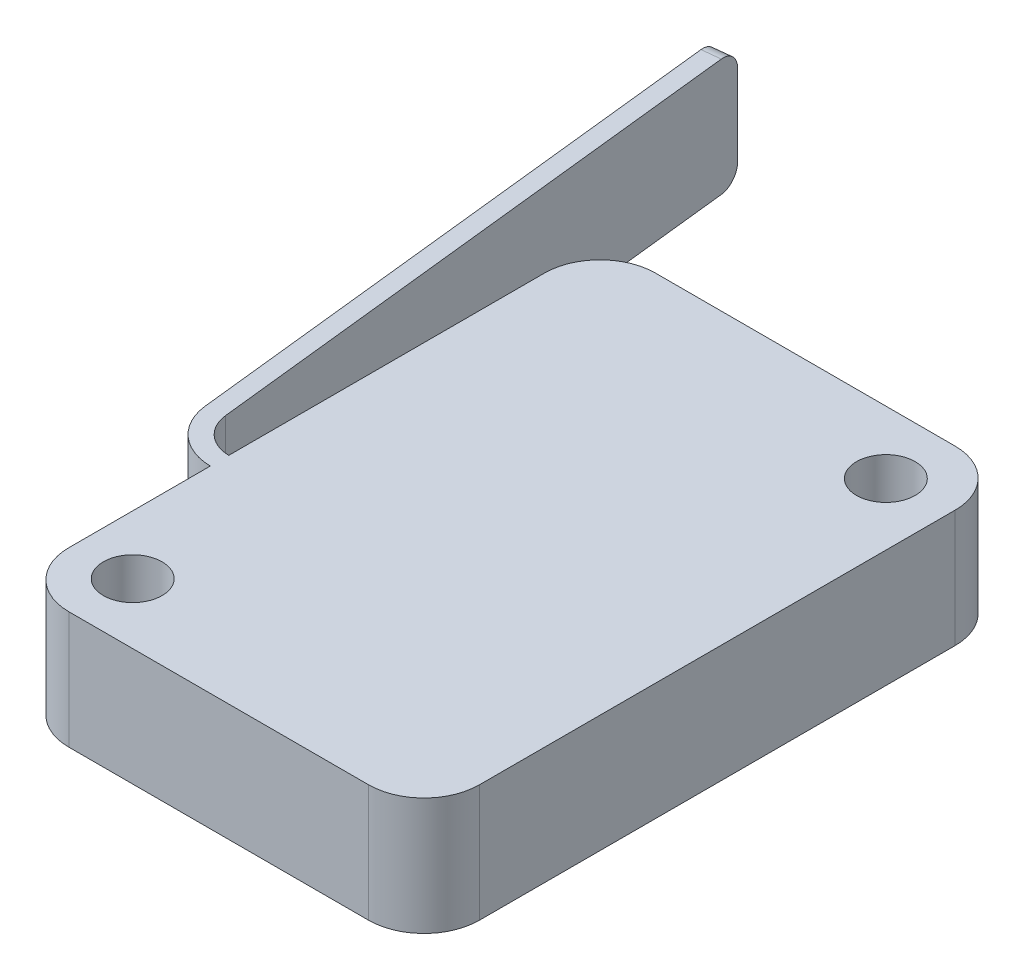
SolidWorks part; units mm, degrees
ref_plane "Front Plane" through (0, 0, 0) normal (0, 0, 1) x (1, 0, 0)
ref_plane "Top Plane" through (0, 0, 0) normal (0, 1, 0) x (1, 0, 0)
ref_plane "Right Plane" through (0, 0, 0) normal (1, 0, 0) x (0, 0, -1)
sketch "Sketch1" plane through (0, 0, 0) normal (0, 1, 0) x (1, 0, 0)
  line L1 (-11.1125, -15.875) -> (11.1125, -15.875)
  line L2 (-11.1125, -15.875) -> (-11.1125, 15.875)
  line L3 (-11.1125, 15.875) -> (11.1125, 15.875)
  line L4 (11.1125, -15.875) -> (11.1125, 15.875)
  line L5 (-11.1125, -15.875) -> (11.1125, 15.875) construction
  line L6 (-11.1125, 15.875) -> (11.1125, -15.875) construction
  point P0 (0, 0)
  dimension "D1" = 31.75
  dimension "D2" = 22.225
extrude "Boss-Extrude1" add sketch "Sketch1" along normal blind 6.35
fillet "Fillet1" radius 3 4 edges at (11.1125, 3.175, -15.875) (-11.1125, 3.175, -15.875) (11.1125, 3.175, 15.875) (-11.1125, 3.175, 15.875)
sketch "Sketch2" plane through (0, 6.35, 0) normal (0, 1, 0) x (1, 0, 0)
  line L1 (11.1125, -12.875) -> (11.1125, -15.875) construction
  line L2 (11.1125, -15.875) -> (8.1125, -15.875) construction
  line L3 (11.1125, -15.875) -> (-17.4625, 28.575) construction
  line L4 (-8.1125, -15.875) -> (8.1125, -15.875) construction
  line L6 (-17.4625, 28.575) -> (-14.0584, -2.5432)
  line L7 (-11.0762, -5.217) -> (-6.2239, -5.217)
  line L8 (-16.4684, 28.6837) -> (-13.0644, -2.4345)
  line L9 (-11.0762, -4.217) -> (-6.2239, -4.217)
  line L10 (-17.4625, 28.575) -> (-16.4684, 28.6837)
  line L11 (-6.2239, -4.217) -> (-6.2239, -5.217)
  arc A0 (8.1125, -15.875) -> (11.1125, -12.875) centre (8.1125, -12.875) ccw construction
  arc A1 (-14.0584, -2.5432) -> (-11.0762, -5.217) centre (-11.0762, -2.217) ccw
  arc A2 (-13.0644, -2.4345) -> (-11.0762, -4.217) centre (-11.0762, -2.217) ccw
  dimension "D3" = 3
  dimension "D1" = 28.575
  dimension "D2" = 44.45
  dimension "D4" = 1
extrude "Boss-Extrude2" add sketch "Sketch2" against normal blind 6.35
fillet "Fillet2" radius 1 2 edges at (-16.9655, 6.35, -28.6294) (-16.9655, 0, -28.6294)
sketch "Sketch3" plane through (0, 6.35, 0) normal (0, 1, 0) x (1, 0, 0)
  circle A0 centre (7.7562, 12.4784) radius 1.5875
  circle A1 centre (-7.9309, -12.5985) radius 1.5875
  dimension "D1" = 3.175
extrude "Cut-Extrude1" cut sketch "Sketch3" against normal blind 16.35
